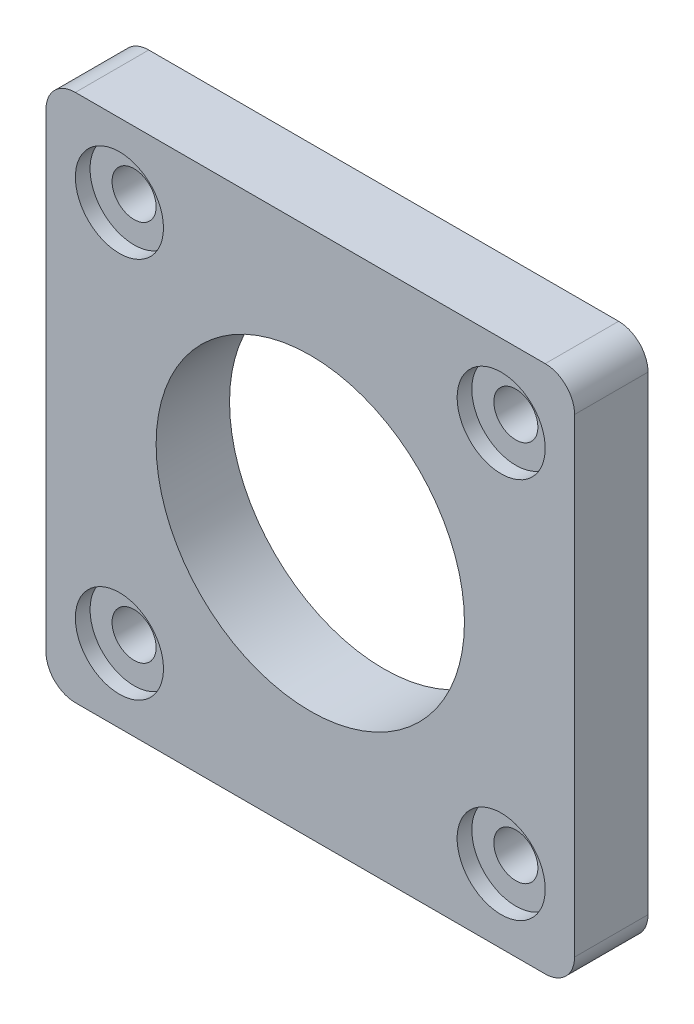
SolidWorks part; units mm, degrees
ref_plane "Front Plane" through (0, 0, 0) normal (0, 0, 1) x (1, 0, 0)
ref_plane "Top Plane" through (0, 0, 0) normal (0, 1, 0) x (1, 0, 0)
ref_plane "Right Plane" through (0, 0, 0) normal (1, 0, 0) x (0, 0, -1)
sketch "Sketch2" plane through (0, 0, 0) normal (0, 0, 1) x (1, 0, 0)
  line L0 (-180, 160) -> (-180, 130) construction
  line L1 (-160, 180) -> (160, 180)
  line L2 (-180, 160) -> (-180, -160)
  line L3 (-160, -180) -> (160, -180)
  line L4 (180, 160) -> (180, -160)
  line L5 (-180, 180) -> (-151.2132, 151.2132) construction
  line L6 (-180, -180) -> (180, 180) construction
  line L7 (0, 180) -> (0, -180) construction
  line L8 (-180, 0) -> (180, 0) construction
  line L9 (-108.7868, 108.7868) -> (174.1421, -174.1421) construction
  circle A0 centre (0, 0) radius 105
  arc A1 (-160, 180) -> (-180, 160) centre (-160, 160) ccw
  arc A2 (160, 180) -> (180, 160) centre (160, 160) cw
  arc A3 (-180, -160) -> (-160, -180) centre (-160, -160) ccw
  arc A4 (180, -160) -> (160, -180) centre (160, -160) cw
  circle A5 centre (-130, 130) radius 30
  circle A6 centre (-130, 130) radius 15
  circle A7 centre (130, 130) radius 30
  circle A8 centre (130, 130) radius 15
  circle A9 centre (130, -130) radius 30
  circle A10 centre (130, -130) radius 15
  circle A11 centre (-130, -130) radius 30
  circle A12 centre (-130, -130) radius 15
  point P0 (0, 0)
  dimension "D3" = 50
  dimension "D1" = 360
  dimension "D2" = 360
extrude "Boss-Extrude1" add sketch "Sketch2" along normal blind 50 contours L2 A3 L3 A4 L4 A2 L1 A1
sketch "Sketch3" plane through (0, 0, 50) normal (0, 0, 1) x (1, 0, 0)
  circle A0 centre (0, 0) radius 105
extrude "Cut-Extrude1" cut sketch "Sketch3" against normal blind 50
sketch "Sketch4" plane through (0, 0, 50) normal (0, 0, 1) x (1, 0, 0)
  line L0 (-180, 160) -> (-180, -160) construction
  line L2 (-76.4193, 180) -> (-210.9174, 180) construction
  line L3 (-160, 180) -> (160, 180) construction
  line L4 (-180, 33.0132) -> (-180, 197.4675) construction
  line L5 (-180, 180) -> (-180, 130)
  line L6 (-180, 130) -> (-130, 130)
  line L7 (0, 0) -> (0, 66.6377) construction
  line L8 (0, 0) -> (-55.0219, 0) construction
  circle A0 centre (-130, 130) radius 15
  circle A1 centre (-130, -130) radius 15
  circle A2 centre (130, -130) radius 15
  circle A3 centre (130, 130) radius 15
extrude "Cut-Extrude3" cut sketch "Sketch4" against normal blind 50 contours A0 | A3 | A2 | A1
sketch "Sketch7" plane through (0, 0, 50) normal (0, 0, 1) x (1, 0, 0)
  line L0 (0, 0) -> (0, 36.6813)
  line L1 (0, 0) -> (-31.1791, 0)
  circle A0 centre (-130, 130) radius 30
  circle A1 centre (130, 130) radius 30
  circle A2 centre (130, -130) radius 30
  circle A3 centre (-130, -130) radius 30
extrude "Cut-Extrude4" cut sketch "Sketch7" against normal blind 10 contours A0 | A1 | A2 | A3
